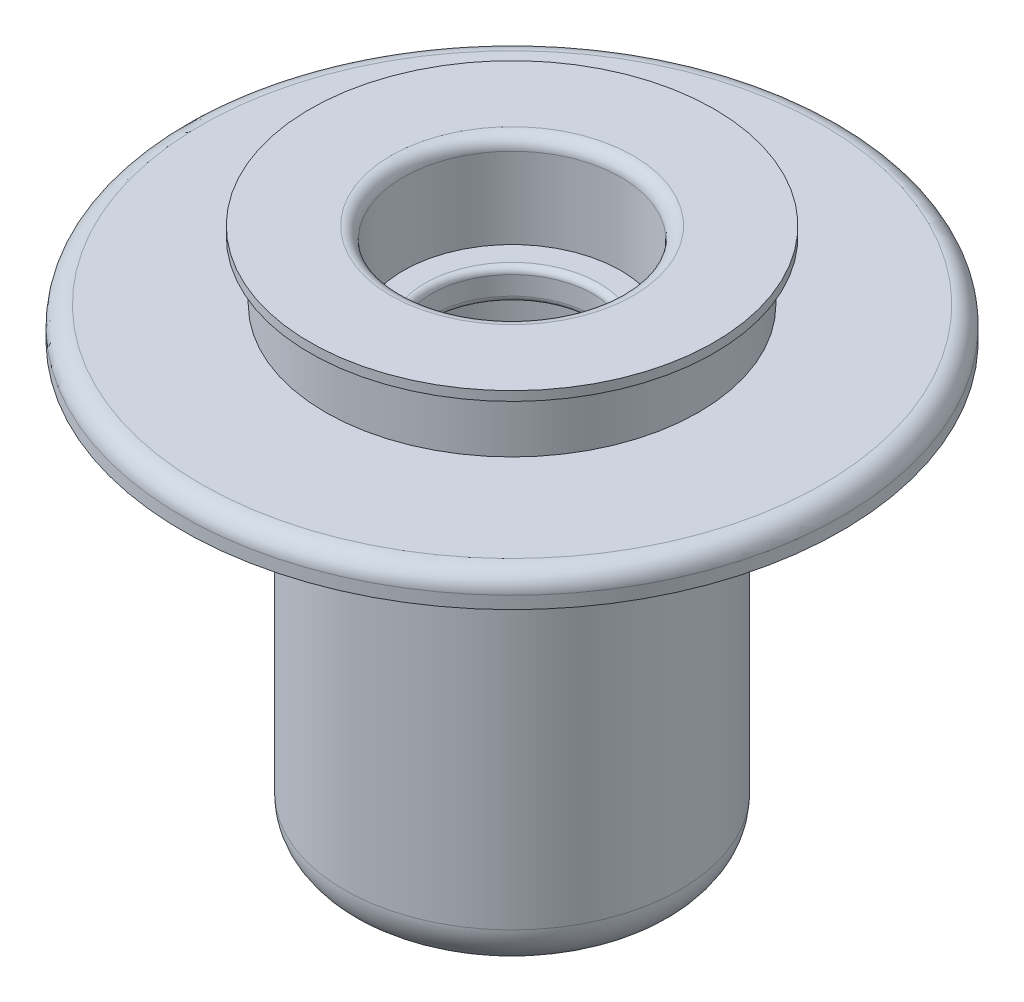
SolidWorks part; units mm, degrees
ref_plane "Plan de face" through (0, 0, 0) normal (0, 0, 1) x (1, 0, 0)
ref_plane "Plan de dessus" through (0, 0, 0) normal (0, 1, 0) x (1, 0, 0)
ref_plane "Plan de droite" through (0, 0, 0) normal (1, 0, 0) x (0, 0, -1)
sketch "Esquisse1" plane through (0, 0, 0) normal (0, 0, 1) x (1, 0, 0)
  line L0 (0, 0) -> (0, 20) construction
  line L1 (19.5, 95.7583) -> (32.5, 95.7583)
  line L2 (27, 79.7583) -> (27, 16.7583)
  line L3 (52.2451, 89.7447) -> (30, 89.7447) construction
  line L4 (32.5, 95.7583) -> (32.5, 94.2583)
  line L5 (20, 9.7583) -> (12.5, 9.7583)
  line L6 (12.5, 9.7583) -> (12.5, 18.7583)
  line L7 (13.5, 19.7583) -> (17.5, 19.7583)
  line L8 (17.5, 19.7583) -> (17.5, 30.7583)
  line L9 (17.5, 30.7583) -> (14, 30.7583)
  line L10 (13, 31.7583) -> (13, 34.7583)
  line L11 (14, 80.7583) -> (17.5, 80.7583)
  line L12 (17.5, 80.7583) -> (17.5, 93.7583)
  line L13 (32.5, 94.2583) -> (30, 94.2583)
  line L14 (14, 75.7583) -> (22, 75.7583)
  line L15 (30, 94.2583) -> (30, 84.7583)
  line L16 (22, 75.7583) -> (22, 35.7583)
  line L17 (22, 35.7583) -> (14, 35.7583)
  line L18 (13, 76.7583) -> (13, 79.7583)
  line L19 (27, 79.7583) -> (53, 79.7583)
  line L20 (53, 79.7583) -> (53, 81.7583)
  line L21 (50, 84.7583) -> (30, 84.7583)
  arc A0 (27, 16.7583) -> (20, 9.7583) centre (20, 16.7583) cw
  arc A1 (19.5, 95.7583) -> (17.5, 93.7583) centre (19.5, 93.7583) ccw
  arc A2 (12.5, 18.7583) -> (13.5, 19.7583) centre (13.5, 18.7583) cw
  arc A3 (13, 79.7583) -> (14, 80.7583) centre (14, 79.7583) cw
  arc A4 (13, 76.7583) -> (14, 75.7583) centre (14, 76.7583) ccw
  arc A5 (13, 31.7583) -> (14, 30.7583) centre (14, 31.7583) ccw
  arc A6 (13, 34.7583) -> (14, 35.7583) centre (14, 34.7583) cw
  arc A7 (53, 81.7583) -> (50, 84.7583) centre (50, 81.7583) ccw
  point P3 (52.2451, 89.7447)
  point P28 (17.5, 95.7583)
  point P31 (12.5, 19.7583)
  point P34 (13, 80.7583)
  point P37 (13, 75.7583)
  point P40 (13, 30.7583)
  point P43 (13, 35.7583)
  point P48 (53, 84.7583)
  dimension "D17" = 13
  dimension "D18" = 2
  dimension "D19" = 1
  dimension "D9" = 7
  dimension "D11" = 3
  dimension "D1" = 50
  dimension "D2" = 11
  dimension "D3" = 15
  dimension "D4" = 5
  dimension "D5" = 4.5
  dimension "D6" = 4.5
  dimension "D7" = 13
  dimension "D8" = 5
  dimension "D10" = 10
  dimension "D12" = 30
  dimension "D13" = 1.5
  dimension "D14" = 5
  dimension "D15" = 5
  dimension "D16" = 9
  dimension "D20" = 86
  dimension "D21" = 5
  dimension "D22" = 53
revolve "Révolution1" add sketch "Esquisse1" angle 360 about L0
sketch "Esquisse4" plane through (0, 0, 0) normal (0, 0, 1) x (1, 0, 0)
  line L0 (0, 0) -> (0, 44.9882) construction
  line L2 (19, 19.25) -> (-19, 19.25)
  line L3 (19, 19.25) -> (19, 30.75)
  line L4 (19, 30.75) -> (-19, 30.75)
  line L5 (-19, 19.25) -> (-19, 30.75)
  line L6 (19, 19.25) -> (-19, 30.75) construction
  line L7 (19, 30.75) -> (-19, 19.25) construction
  point P3 (0, 25)
  point P4 (0, 25)
  dimension "D1" = 25
  dimension "D2" = 11.5
  dimension "D3" = 38
extrude "Enlèv. mat.-Extru.1" cut sketch "Esquisse4" against normal blind 40
